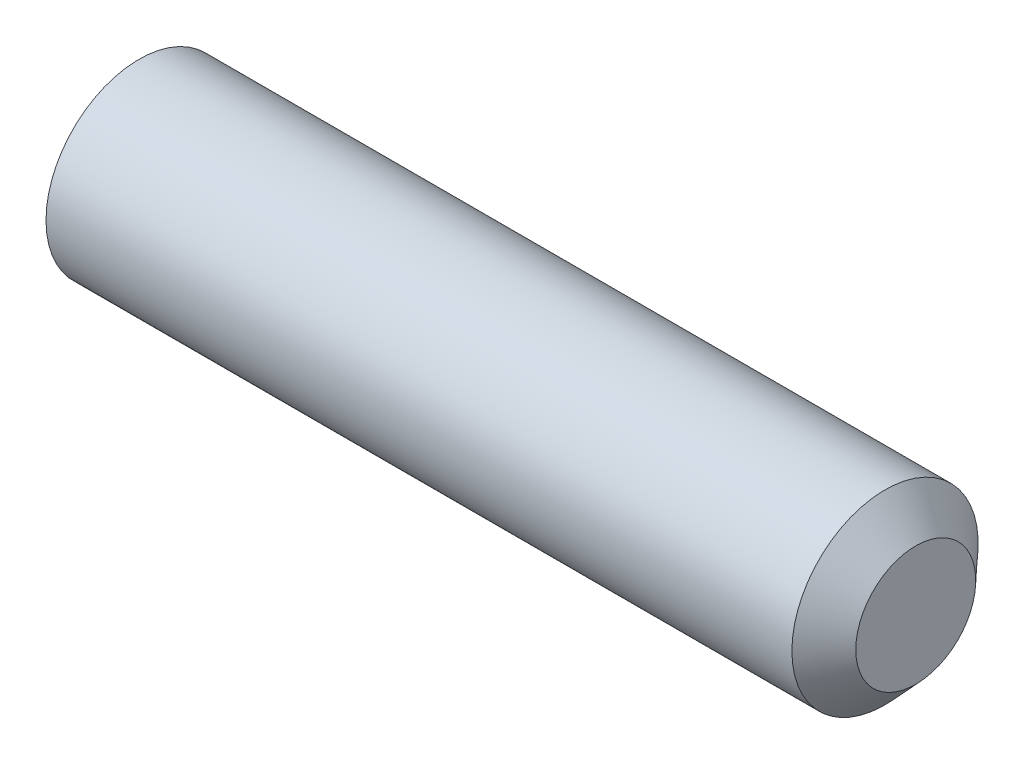
SolidWorks part; units mm, degrees
ref_plane "Front Plane" through (0, 0, 0) normal (0, 0, 1) x (1, 0, 0)
ref_plane "Top Plane" through (0, 0, 0) normal (0, 1, 0) x (1, 0, 0)
ref_plane "Right Plane" through (0, 0, 0) normal (1, 0, 0) x (0, 0, -1)
sketch "Sketch1" plane through (0, 0, 0) normal (0, 1, 0) x (1, 0, 0)
  line L0 (0, 0) -> (50000, 0) construction
  line L5 (-49.75, 0) -> (-49.75, 12.425)
  line L6 (-49.75, 12.425) -> (49.75, 12.425)
  line L7 (-49.75, 0) -> (53.85, 0)
  line L8 (49.75, 12.425) -> (53.85, 8)
  line L9 (53.85, 8) -> (53.85, 0)
  point P5 (0, 12.425)
  dimension "D1" = 12.425
  dimension "D2" = 99.5
  dimension "D3" = 103.6
  dimension "D4" = 8
revolve "Revolve1" add sketch "Sketch1" angle 360 about L0
